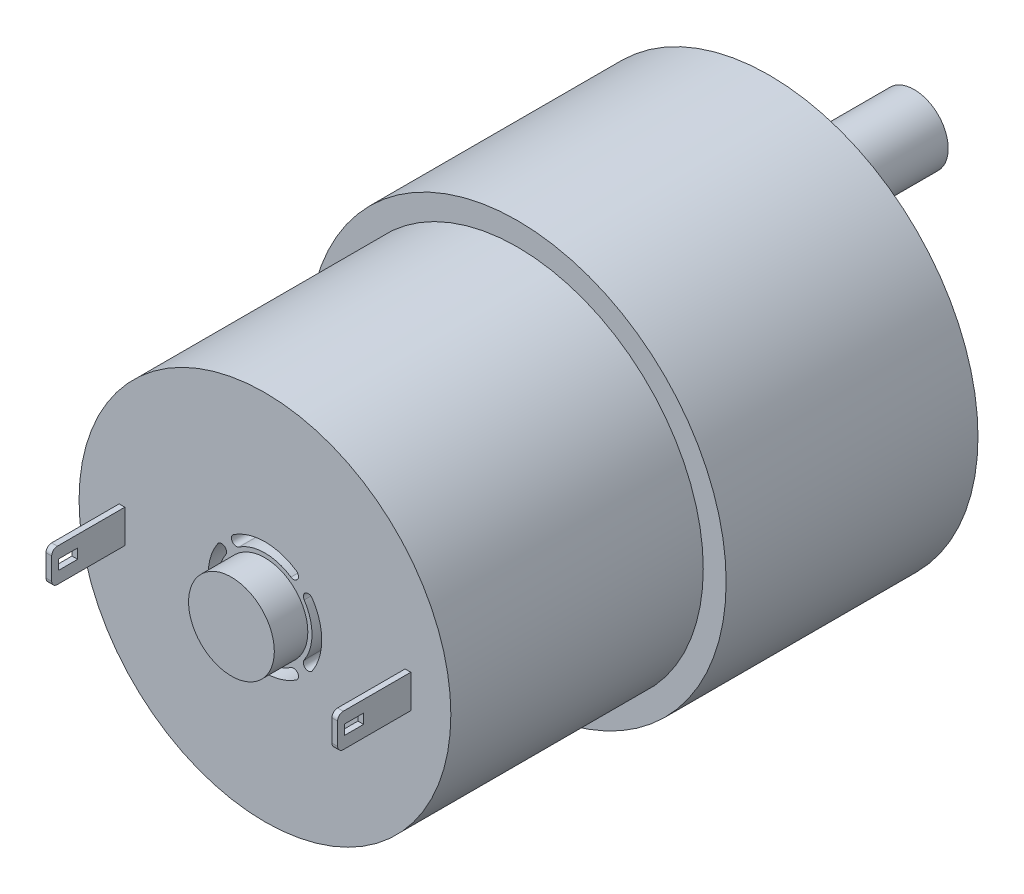
SolidWorks part; units mm, degrees
ref_plane "Спереди" through (0, 0, 0) normal (0, 0, 1) x (1, 0, 0)
ref_plane "Сверху" through (0, 0, 0) normal (0, 1, 0) x (1, 0, 0)
ref_plane "Справа" through (0, 0, 0) normal (1, 0, 0) x (0, 0, -1)
sketch "Эскиз1" plane through (0, 0, 0) normal (0, 0, 1) x (1, 0, 0)
  circle A0 centre (0, 0) radius 18.38
  dimension "D1" = 36.76
extrude "Бобышка-Вытянуть1" add sketch "Эскиз1" along normal blind 22.17
sketch "Эскиз2" plane through (0, 0, 22.17) normal (0, 0, 1) x (1, 0, 0)
  circle A0 centre (0, 0) radius 16.365
  dimension "D1" = 32.73
extrude "Бобышка-Вытянуть2" add sketch "Эскиз2" along normal blind 22.22
sketch "Эскиз3" plane through (0, 0, 0) normal (0, 0, -1) x (-1, 0, 0)
  line L0 (18.38, 0) -> (13.88, 0) construction
  line L1 (13.88, 0) -> (1.92, 0) construction
  circle A0 centre (0, 0) radius 18.38 construction
  circle A1 centre (7.9, 0) radius 5.98
  dimension "D1" = 4.5
  dimension "D2" = 11.96
extrude "Бобышка-Вытянуть3" add sketch "Эскиз3" along normal blind 5.7
sketch "Эскиз4" plane through (0, 0, -5.7) normal (0, 0, -1) x (-1, 0, 0)
  circle A0 centre (7.9, 0) radius 3
  dimension "D1" = 6
extrude "Бобышка-Вытянуть4" add sketch "Эскиз4" along normal blind 14.96
sketch "Эскиз5" plane through (0, 0, -20.66) normal (0, 0, -1) x (-1, 0, 0)
  line L0 (4.9, 0) -> (10.39, 0) construction
  line L1 (10.39, 2.0565) -> (10.39, -2.5925)
  line L2 (10.39, -2.5925) -> (11.6948, -2.5925)
  line L3 (11.6948, -2.5925) -> (11.6948, 2.0565)
  line L4 (11.6948, 2.0565) -> (10.39, 2.0565)
  circle A0 centre (7.9, 0) radius 3 construction
  circle A1 centre (7.9, 0) radius 3 construction
  dimension "D1" = 5.49
extrude "Вырез-Вытянуть1" cut sketch "Эскиз5" against normal blind 12
sketch "Эскиз6" plane through (0, 0, 0) normal (0, 0, -1) x (-1, 0, 0)
  line L0 (0, -18.38) -> (0, -16.86) construction
  line L1 (0, -16.86) -> (0, -14.35) construction
  circle A1 centre (0, 0) radius 18.38 construction
  circle A2 centre (0, -15.605) radius 1.255
  circle A3 centre (-13.5143, -7.8025) radius 1.255
  circle A4 centre (-13.5143, 7.8025) radius 1.255
  circle A5 centre (0, 15.605) radius 1.255
  circle A6 centre (13.5143, 7.8025) radius 1.255
  circle A7 centre (13.5143, -7.8025) radius 1.255
  point P23 (0, 0)
  dimension "D1" = 1.52
  dimension "D2" = 2.51
  dimension "D3" = 6
extrude "Вырез-Вытянуть2" cut sketch "Эскиз6" against normal blind 3
sketch "Эскиз7" plane through (0, 0, 0) normal (0, 0, -1) x (-1, 0, 0)
  arc A0 (7.9, 6.7311) -> (7.9, -6.7311) centre (7.9, 0) ccw
  arc A1 (7.9, 6.7311) -> (7.9, -6.7311) centre (-2.1196, 0) ccw
extrude "Вырез-Вытянуть3" cut sketch "Эскиз7" against normal blind 1
fillet "Скругление1" radius 0.5 2 edges at (-1.1689, 0, 1) (14.1902, 0, 1)
fillet "Скругление3" radius 0.5 1 edges at (-13.88, 0, -5.7)
sketch "Эскиз8" plane through (0, 0, 44.39) normal (0, 0, 1) x (1, 0, 0)
  line L0 (-16.365, 0) -> (-12.585, 0) construction
  line L1 (0, -16.365) -> (0, -21.7411) construction
  line L2 (-12.835, -1.465) -> (-12.335, -1.465)
  line L3 (-12.835, -1.465) -> (-12.835, 1.465)
  line L4 (-12.835, 1.465) -> (-12.335, 1.465)
  line L5 (-12.335, -1.465) -> (-12.335, 1.465)
  line L6 (-12.835, -1.465) -> (-12.335, 1.465) construction
  line L7 (-12.835, 1.465) -> (-12.335, -1.465) construction
  line L8 (12.835, 1.465) -> (12.335, 1.465)
  line L9 (12.335, -1.465) -> (12.335, 1.465)
  line L10 (12.835, -1.465) -> (12.335, -1.465)
  line L11 (12.835, -1.465) -> (12.835, 1.465)
  circle A0 centre (0, 0) radius 16.365 construction
  dimension "D1" = 3.78
  dimension "D2" = 2.93
  dimension "D3" = 0.5
extrude "Бобышка-Вытянуть5" add sketch "Эскиз8" along normal blind 6.44
sketch "Эскиз9" plane through (0, 0, 44.39) normal (0, 0, 1) x (1, 0, 0)
  circle A0 centre (0, 0) radius 3.775
  dimension "D1" = 7.55
extrude "Бобышка-Вытянуть6" add sketch "Эскиз9" along normal blind 2.95
sketch "Эскиз10" plane through (0, 0, 44.39) normal (0, 0, 1) x (1, 0, 0)
  line L0 (-4.9982, 0) -> (-6.1684, 0) construction
  arc A0 (-4.1665, 2.7609) -> (-4.1665, -2.7609) centre (0, 0) ccw
  arc A1 (-3.4518, 2.2885) -> (-3.4518, -2.2885) centre (0, 0) ccw
  arc A2 (-4.1665, -2.7609) -> (-3.4518, -2.2885) centre (-3.8094, -2.5243) ccw
  arc A3 (-4.1665, 2.7609) -> (-3.4518, 2.2885) centre (-3.8094, 2.5243) cw
  arc A4 (2.7609, 4.1665) -> (-2.7609, 4.1665) centre (0, 0) ccw
  arc A5 (-2.7609, 4.1665) -> (-2.2885, 3.4518) centre (-2.5243, 3.8094) ccw
  arc A6 (2.2885, 3.4518) -> (-2.2885, 3.4518) centre (0, 0) ccw
  arc A7 (2.7609, 4.1665) -> (2.2885, 3.4518) centre (2.5243, 3.8094) cw
  arc A8 (4.1665, -2.7609) -> (4.1665, 2.7609) centre (0, 0) ccw
  arc A9 (4.1665, 2.7609) -> (3.4518, 2.2885) centre (3.8094, 2.5243) ccw
  arc A10 (3.4518, -2.2885) -> (3.4518, 2.2885) centre (0, 0) ccw
  arc A11 (4.1665, -2.7609) -> (3.4518, -2.2885) centre (3.8094, -2.5243) cw
  arc A12 (-2.7609, -4.1665) -> (2.7609, -4.1665) centre (0, 0) ccw
  arc A13 (2.7609, -4.1665) -> (2.2885, -3.4518) centre (2.5243, -3.8094) ccw
  arc A14 (-2.2885, -3.4518) -> (2.2885, -3.4518) centre (0, 0) ccw
  arc A15 (-2.7609, -4.1665) -> (-2.2885, -3.4518) centre (-2.5243, -3.8094) cw
  point P4 (-4.1415, 0)
  point P32 (0, 0)
  dimension "D1" = 4
extrude "Вырез-Вытянуть4" cut sketch "Эскиз10" against normal blind 2.95 contours A0 A2 A1 A3 | A12 A13 A14 A15 | A4 A5 A6 A7 | A8 A9 A10 A11
sketch "Эскиз11" plane through (-12.835, 0, 0) normal (-1, 0, 0) x (0, 0, 1)
  line L1 (50.2235, -0.4331) -> (48.5426, -0.4331)
  line L2 (50.2235, -0.4331) -> (50.2235, 0.4331)
  line L3 (50.2235, 0.4331) -> (48.5426, 0.4331)
  line L4 (48.5426, -0.4331) -> (48.5426, 0.4331)
  line L5 (50.2235, -0.4331) -> (48.5426, 0.4331) construction
  line L6 (50.2235, 0.4331) -> (48.5426, -0.4331) construction
  point P0 (49.383, 0)
extrude "Вырез-Вытянуть5" cut sketch "Эскиз11" against normal blind 37.95
fillet "Скругление4" radius 0.5 4 edges at (12.585, 1.465, 50.83) (12.585, -1.465, 50.83) (-12.585, -1.465, 50.83) (-12.585, 1.465, 50.83)
